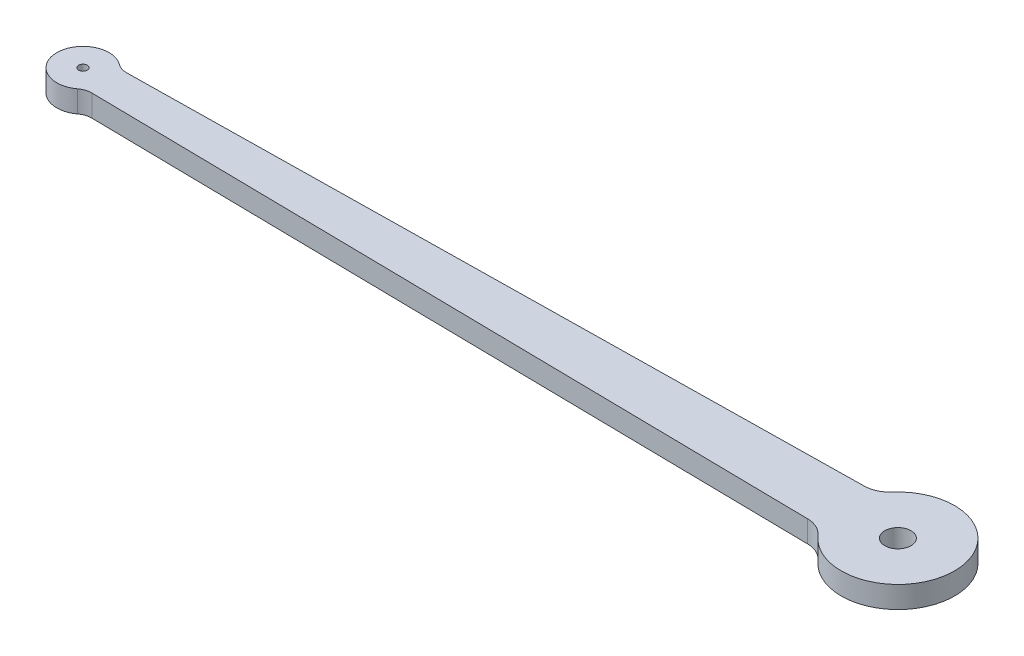
SolidWorks part; units mm, degrees
material "6061 Alloy"
ref_plane "Front Plane" through (0, 0, 0) normal (0, 0, 1) x (1, 0, 0)
ref_plane "Top Plane" through (0, 0, 0) normal (0, 1, 0) x (1, 0, 0)
ref_plane "Right Plane" through (0, 0, 0) normal (1, 0, 0) x (0, 0, -1)
sketch "Sketch1" plane through (0, 0, 0) normal (0, 1, 0) x (1, 0, 0)
  line L0 (-46.75, 0) -> (46.75, 0) construction
  line L1 (39.6401, 3.25) -> (-43.7197, 2)
  line L2 (39.6401, -3.25) -> (-43.7197, -2)
  line L3 (39.6401, 3.25) -> (39.6401, -3.25) construction
  line L4 (0, 0) -> (39.6401, 0) construction
  line L5 (-43.7197, 2) -> (-43.7197, -2) construction
  line L6 (0, 0) -> (-43.7197, 0) construction
  arc A0 (41.8546, -4.2761) -> (41.8546, 4.2761) centre (46.75, 0) ccw
  arc A1 (-44.9498, 2.3999) -> (-44.9498, -2.3999) centre (-46.75, 0) ccw
  arc A2 (39.6401, -3.25) -> (41.8546, -4.2761) centre (39.5952, -6.2497) cw
  arc A3 (-43.7197, -2) -> (-44.9498, -2.3999) centre (-43.7497, -3.9998) ccw
  arc A4 (-43.7197, 2) -> (-44.9498, 2.3999) centre (-43.7497, 3.9998) cw
  arc A5 (39.6401, 3.25) -> (41.8546, 4.2761) centre (39.5952, 6.2497) ccw
  dimension "D1" = 13
  dimension "D2" = 6
  dimension "D6" = 2
  dimension "D7" = 3
  dimension "D3" = 93.5
  dimension "D4" = 4
  dimension "D5" = 6.5
extrude "Boss-Extrude1" add sketch "Sketch1" along normal blind 2.5
sketch "Sketch2" plane through (0, 2.5, 0) normal (0, 1, 0) x (1, 0, 0)
  circle A0 centre (-46.75, 0) radius 0.5
  circle A1 centre (46.75, 0) radius 1.5
  dimension "D1" = 1
  dimension "D2" = 3
extrude "Cut-Extrude1" cut sketch "Sketch2" against normal up to next contours A0 | A1
ref_plane "Central Mate Plane" through (0, 1.25, 0) normal (0, 1, 0) x (-1, 0, 0)
